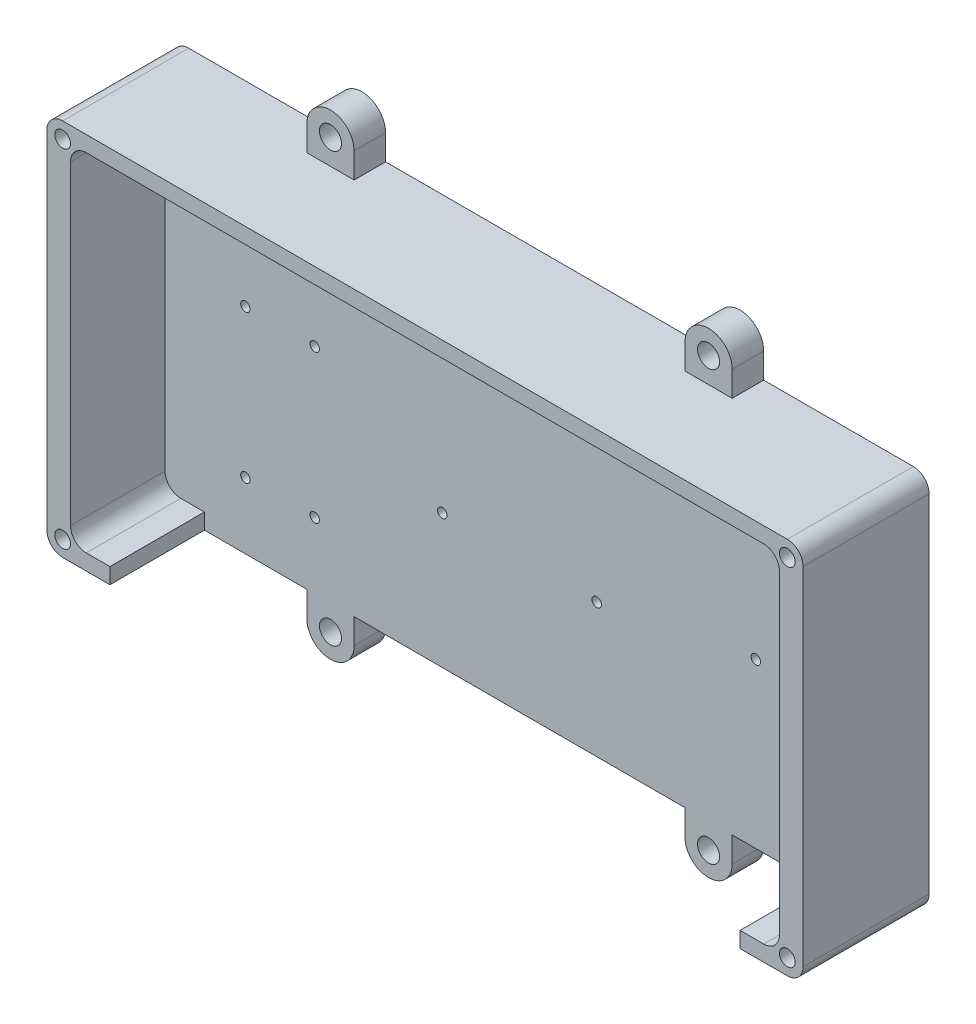
SolidWorks part; units mm, degrees
ref_plane "Front Plane" through (0, 0, 0) normal (0, 0, 1) x (1, 0, 0)
ref_plane "Top Plane" through (0, 0, 0) normal (0, 1, 0) x (1, 0, 0)
ref_plane "Right Plane" through (0, 0, 0) normal (1, 0, 0) x (0, 0, -1)
sketch "Sketch2" plane through (0, 0, 0) normal (0, 0, 1) x (1, 0, 0)
  line L0 (-120, 0) -> (0, 0) construction
  line L1 (0, 0) -> (0, 60) construction
  line L2 (52.5, 60) -> (-52.5, 60)
  line L3 (-120, 55) -> (-120, -55)
  line L4 (-60, 50) -> (-60, 68) construction
  line L5 (-67.5, 60) -> (-67.5, 68)
  line L6 (-52.5, 60) -> (-52.5, 68)
  line L7 (-67.5, 60) -> (-115, 60)
  line L8 (-67.5, -60) -> (-115, -60)
  line L9 (-67.5, -60) -> (-67.5, -68)
  line L10 (-52.5, -60) -> (-52.5, -68)
  line L11 (52.5, -60) -> (-52.5, -60)
  line L12 (52.5, -60) -> (52.5, -68)
  line L13 (67.5, -60) -> (67.5, -68)
  line L14 (67.5, -60) -> (115, -60)
  line L15 (120, 55) -> (120, -55)
  line L16 (60, 50) -> (60, 68) construction
  line L17 (67.5, 60) -> (115, 60)
  line L18 (52.5, 60) -> (52.5, 68)
  line L19 (67.5, 60) -> (67.5, 68)
  arc A1 (-52.5, 68) -> (-67.5, 68) centre (-60, 68) ccw
  arc A2 (-115, 60) -> (-120, 55) centre (-115, 55) ccw
  arc A3 (-115, -60) -> (-120, -55) centre (-115, -55) cw
  arc A4 (-52.5, -68) -> (-67.5, -68) centre (-60, -68) cw
  arc A5 (52.5, -68) -> (67.5, -68) centre (60, -68) ccw
  arc A6 (115, -60) -> (120, -55) centre (115, -55) ccw
  arc A7 (115, 60) -> (120, 55) centre (115, 55) cw
  arc A8 (52.5, 68) -> (67.5, 68) centre (60, 68) cw
  point P7 (-60.5, 60)
  point P10 (-120, 60)
  point P31 (0, -60)
  point P41 (120, 60)
  point P42 (60.5, 60)
  dimension "D5" = 7.5
  dimension "D7" = 5
  dimension "D1" = 120
  dimension "D2" = 60
  dimension "D3" = 60
  dimension "D4" = 15
  dimension "D6" = 8
extrude "Boss-Extrude1" add sketch "Sketch2" along normal blind 10
sketch "Sketch3" plane through (0, 0, 10) normal (0, 0, 1) x (1, 0, 0)
  line L0 (0, 57.5317) -> (0, -73.3093) construction
  line L1 (-117.8606, 0) -> (110.838, 0) construction
  circle A0 centre (-60, 68) radius 3.5
  arc A1 (-52.5, 68) -> (-67.5, 68) centre (-60, 68) ccw construction
  circle A2 centre (-60, -68) radius 3.5
  circle A3 centre (60, -68) radius 3.5
  circle A4 centre (60, 68) radius 3.5
  dimension "D1" = 7
extrude "izvrtina_vijacenje_nosilca_m7" cut sketch "Sketch3" against normal blind 10
sketch "Sketch7" plane through (0, 0, 10) normal (0, 0, 1) x (1, 0, 0)
  line L1 (-115, -60) -> (115, -60)
  line L2 (-112.5, 55) -> (-112.5, -55)
  line L3 (-112.5, 50) -> (-112.5, -50)
  line L4 (-107.5, -55) -> (107.5, -55)
  line L5 (112.5, -55) -> (112.5, 55)
  line L6 (112.5, -50) -> (112.5, 50)
  line L7 (-107.5, 55) -> (107.5, 55)
  line L8 (-52.5, -60) -> (52.5, -60) construction
  line L9 (-120, 55) -> (-120, -55)
  line L10 (0, 67.3171) -> (0, -78.2792) construction
  line L11 (-115, 60) -> (115, 60)
  line L12 (120, 55) -> (120, -55)
  line L13 (52.5, 60) -> (-52.5, 60) construction
  line L14 (-120, 55) -> (-120, -55) construction
  arc A0 (107.5, 55) -> (112.5, 50) centre (107.5, 50) cw
  arc A1 (107.5, -55) -> (112.5, -50) centre (107.5, -50) ccw
  arc A2 (-107.5, -55) -> (-112.5, -50) centre (-107.5, -50) cw
  arc A3 (-107.5, 55) -> (-112.5, 50) centre (-107.5, 50) ccw
  arc A4 (-115, 60) -> (-120, 55) centre (-115, 55) ccw
  arc A5 (-120, -55) -> (-115, -60) centre (-115, -55) ccw
  arc A6 (-115, 60) -> (-120, 55) centre (-115, 55) ccw construction
  arc A7 (-120, -55) -> (-115, -60) centre (-115, -55) ccw construction
  arc A8 (120, -55) -> (115, -60) centre (115, -55) cw
  arc A9 (115, 60) -> (120, 55) centre (115, 55) cw
  point P40 (0, -60)
  point P45 (0, 60)
  dimension "D3" = 5
  dimension "D1" = 7.5
  dimension "D2" = 7.5
extrude "Boss-Extrude2" add sketch "Sketch7" along normal blind 30
sketch "Sketch8" plane through (0, -60, 0) normal (0, -1, 0) x (1, 0, 0)
  line L0 (0, 89.2514) -> (0, -9.2514) construction
  line L1 (-100, 40) -> (100, 40)
  line L2 (-100, 40) -> (-100, 10)
  line L3 (-100, 10) -> (100, 10)
  line L4 (100, 40) -> (100, 10)
  line L7 (-115, 40) -> (115, 40) construction
  line L8 (-52.5, 0) -> (52.5, 0) construction
  point P4 (0, 40)
  dimension "D1" = 100
  dimension "D2" = 0
  dimension "D3" = 10
extrude "izvrtina_kabli" cut sketch "Sketch8" against normal blind 5
sketch "Sketch10" plane through (0, 0, 10) normal (0, 0, 1) x (1, 0, 0)
  line L1 (-24.5, 40.5) -> (24.5, 40.5) construction
  line L2 (-24.5, 40.5) -> (-24.5, -17.5) construction
  line L3 (-24.5, -17.5) -> (24.5, -17.5) construction
  line L4 (24.5, 40.5) -> (24.5, -17.5) construction
  circle A0 centre (24.5, 40.5) radius 1.5
  circle A1 centre (24.5, -17.5) radius 1.5
  circle A2 centre (-24.5, -17.5) radius 1.5
  circle A3 centre (-24.5, 40.5) radius 1.5
  point P4 (0, 40.5)
  dimension "D4" = 3
  dimension "D1" = 58
  dimension "D2" = 49
  dimension "D3" = 40.5
extrude "izvrtine_rpi_m2.5_heat_insert" cut sketch "Sketch10" against normal blind 10
sketch "Sketch11" plane through (0, 0, 10) normal (0, 0, 1) x (1, 0, 0)
  line L1 (-87, 8) -> (-65, 8) construction
  line L2 (-87, 8) -> (-87, -39) construction
  line L3 (-87, -39) -> (-65, -39) construction
  line L4 (-65, 8) -> (-65, -39) construction
  circle A0 centre (-87, 8) radius 1.5
  circle A1 centre (-65, 8) radius 1.5
  circle A2 centre (-65, -39) radius 1.5
  circle A3 centre (-87, -39) radius 1.5
  dimension "D5" = 3
  dimension "D1" = 22
  dimension "D2" = 47
  dimension "D3" = 65
  dimension "D4" = 8
extrude "izvrtine_buck_m2_heat_inserts" cut sketch "Sketch11" against normal blind 10
sketch "Sketch12" plane through (0, 0, 10) normal (0, 0, 1) x (1, 0, 0)
  line L0 (75, 47.9004) -> (75, -41.5038) construction
  circle A0 centre (75, 34) radius 1.5
  circle A1 centre (75, -8) radius 1.5
  dimension "D4" = 3
  dimension "D1" = 75
  dimension "D2" = 8
  dimension "D3" = 42
extrude "izvrtine_uno_m2.5_heat_insert" cut sketch "Sketch12" against normal blind 10
sketch "Sketch14" plane through (0, 0, 40) normal (0, 0, 1) x (1, 0, 0)
  line L0 (0, 72.6557) -> (0, -109.8258) construction
  line L1 (-174.4536, 0) -> (181.629, 0) construction
  circle A0 centre (-115, 55) radius 2.5
  arc A1 (-115, 60) -> (-120, 55) centre (-115, 55) ccw construction
  circle A2 centre (115, 55) radius 2.5
  circle A3 centre (115, -55) radius 2.5
  circle A4 centre (-115, -55) radius 2.5
  dimension "D1" = 5
extrude "izvrtine_top_m4_heat_insert" cut sketch "Sketch14" against normal blind 6
